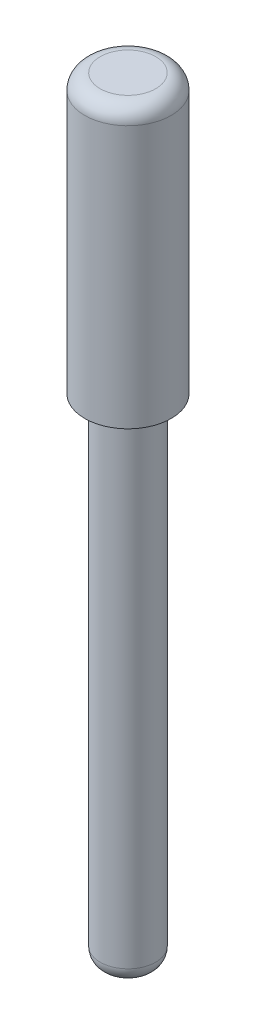
SolidWorks part; units mm, degrees
ref_plane "前视基准面" through (0, 0, 0) normal (0, 0, 1) x (1, 0, 0)
ref_plane "上视基准面" through (0, 0, 0) normal (0, 1, 0) x (1, 0, 0)
ref_plane "右视基准面" through (0, 0, 0) normal (1, 0, 0) x (0, 0, -1)
sketch "草图1" plane through (0, 0, 0) normal (0, 1, 0) x (1, 0, 0)
  circle A0 centre (0, 0) radius 1.4
  dimension "D1" = 2.8
extrude "凸台-拉伸1" add sketch "草图1" along normal blind 25
sketch "草图2" plane through (0, 0, 0) normal (1, 0, 0) x (0, 0, -1)
  line L0 (0, 0) -> (0, -50000) construction
  line L1 (1.4, 0) -> (0.9, 0)
  line L2 (1.4, 0) -> (1.4, 16)
  line L3 (1.4, 16) -> (0.9, 16)
  line L4 (0.9, 0) -> (0.9, 16)
  line L5 (1.4, 25) -> (-1.4, 25) construction
  dimension "D1" = 1.8
  dimension "D2" = 9
revolve "切除-旋转1" cut sketch "草图2" angle 360 about L0
fillet "圆角1" radius 0.5 2 edges at (0, 0, 0.9) (0, 25, 1.4)
